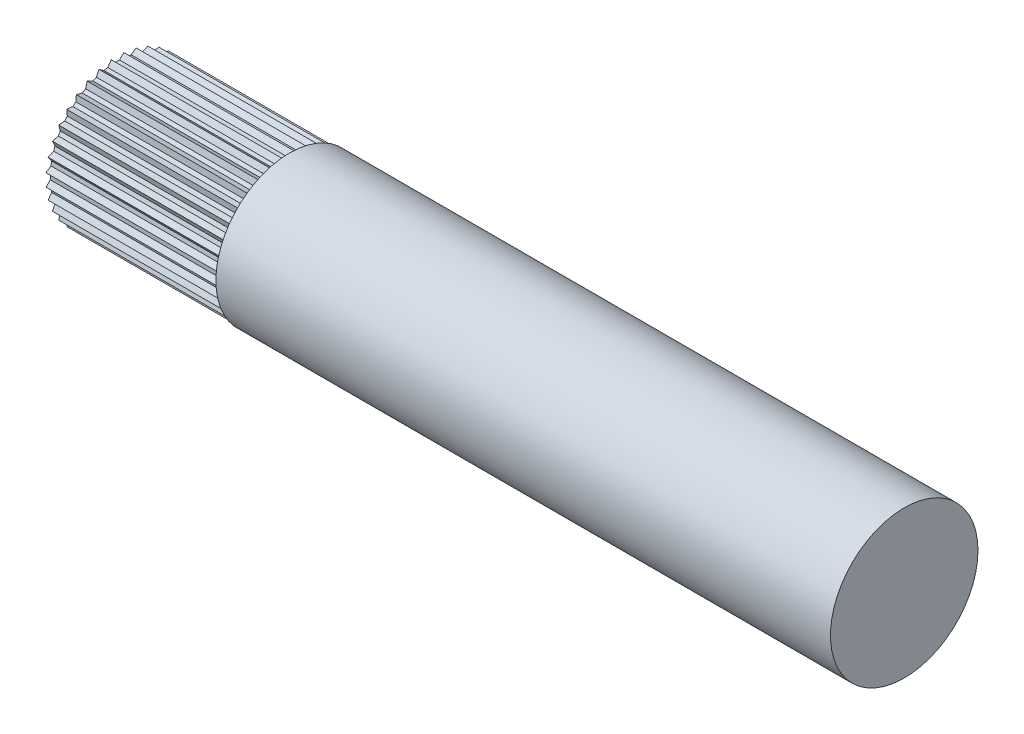
SolidWorks part; units mm, degrees
material "AISI 1020 Steel, Cold Rolled"
ref_plane "X-Y Datum" through (0, 0, 0) normal (0, 0, 1) x (1, 0, 0)
ref_plane "X-Z Datum" through (0, 0, 0) normal (0, 1, 0) x (1, 0, 0)
ref_plane "Y-Z Datum" through (0, 0, 0) normal (1, 0, 0) x (0, 0, -1)
sketch "Sketch1" plane through (0, 0, 0) normal (0, 1, 0) x (1, 0, 0)
  line L0 (139.925, 9.525) -> (139.925, 7.9375)
  line L1 (139.925, 7.9375) -> (19.25, 7.9375)
  line L2 (19.25, 7.9375) -> (19.25, 9.525)
  line L3 (19.25, 9.525) -> (139.925, 9.525)
  line L6 (157.324, 0) -> (-11.2643, 0) construction
  line L7 (19.25, 9.525) -> (19.25, -9.525) construction
  dimension "D1" = 1.5875
revolve "Revolve1" add sketch "Sketch1" angle 360 about L6
sketch "Sketch4" plane through (0, 0, 0) normal (1, 0, 0) x (0, 0, -1)
  line L0 (-9.2357, 0.808) -> (-8.6817, 0.254)
  line L1 (-8.6817, 0.254) -> (-8.6817, -0.254)
  line L2 (-8.6817, -0.254) -> (-9.2357, -0.808)
  line L3 (-8.6817, 0) -> (0, 0) construction
  line L4 (-8.5939, 1.2574) -> (-9.2357, 0.808)
  line L5 (-8.5057, 1.7577) -> (-8.5939, 1.2574)
  line L6 (-8.9551, 2.3995) -> (-8.5057, 1.7577)
  line L7 (-8.245, 2.7306) -> (-8.9551, 2.3995)
  line L8 (-8.0713, 3.208) -> (-8.245, 2.7306)
  line L9 (-8.4024, 3.9181) -> (-8.0713, 3.208)
  line L10 (-7.6456, 4.1209) -> (-8.4024, 3.9181)
  line L11 (-7.3916, 4.5608) -> (-7.6456, 4.1209)
  line L12 (-7.5944, 5.3176) -> (-7.3916, 4.5608)
  line L13 (-6.8138, 5.3859) -> (-7.5944, 5.3176)
  line L14 (-6.4873, 5.7751) -> (-6.8138, 5.3859)
  line L15 (-6.5556, 6.5556) -> (-6.4873, 5.7751)
  line L16 (-5.7751, 6.4873) -> (-6.5556, 6.5556)
  line L17 (-5.3859, 6.8138) -> (-5.7751, 6.4873)
  line L18 (-5.3176, 7.5944) -> (-5.3859, 6.8138)
  line L19 (-4.5608, 7.3916) -> (-5.3176, 7.5944)
  line L20 (-4.1209, 7.6456) -> (-4.5608, 7.3916)
  line L21 (-3.9181, 8.4024) -> (-4.1209, 7.6456)
  line L22 (-3.208, 8.0713) -> (-3.9181, 8.4024)
  line L23 (-2.7306, 8.245) -> (-3.208, 8.0713)
  line L24 (-2.3995, 8.9551) -> (-2.7306, 8.245)
  line L25 (-1.7577, 8.5057) -> (-2.3995, 8.9551)
  line L26 (-1.2574, 8.5939) -> (-1.7577, 8.5057)
  line L27 (-0.808, 9.2357) -> (-1.2574, 8.5939)
  line L28 (-0.254, 8.6817) -> (-0.808, 9.2357)
  line L29 (0.254, 8.6817) -> (-0.254, 8.6817)
  line L30 (0.808, 9.2357) -> (0.254, 8.6817)
  line L31 (1.2574, 8.5939) -> (0.808, 9.2357)
  line L32 (1.7577, 8.5057) -> (1.2574, 8.5939)
  line L33 (2.3995, 8.9551) -> (1.7577, 8.5057)
  line L34 (2.7306, 8.245) -> (2.3995, 8.9551)
  line L35 (3.208, 8.0713) -> (2.7306, 8.245)
  line L36 (3.9181, 8.4024) -> (3.208, 8.0713)
  line L37 (4.1209, 7.6456) -> (3.9181, 8.4024)
  line L38 (4.5608, 7.3916) -> (4.1209, 7.6456)
  line L39 (5.3176, 7.5944) -> (4.5608, 7.3916)
  line L40 (5.3859, 6.8138) -> (5.3176, 7.5944)
  line L41 (5.7751, 6.4873) -> (5.3859, 6.8138)
  line L42 (6.5556, 6.5556) -> (5.7751, 6.4873)
  line L43 (6.4873, 5.7751) -> (6.5556, 6.5556)
  line L44 (6.8138, 5.3859) -> (6.4873, 5.7751)
  line L45 (7.5944, 5.3176) -> (6.8138, 5.3859)
  line L46 (7.3916, 4.5608) -> (7.5944, 5.3176)
  line L47 (7.6456, 4.1209) -> (7.3916, 4.5608)
  line L48 (8.4024, 3.9181) -> (7.6456, 4.1209)
  line L49 (8.0713, 3.208) -> (8.4024, 3.9181)
  line L50 (8.245, 2.7306) -> (8.0713, 3.208)
  line L51 (8.9551, 2.3995) -> (8.245, 2.7306)
  line L52 (8.5057, 1.7577) -> (8.9551, 2.3995)
  line L53 (8.5939, 1.2574) -> (8.5057, 1.7577)
  line L54 (9.2357, 0.808) -> (8.5939, 1.2574)
  line L55 (8.6817, 0.254) -> (9.2357, 0.808)
  line L56 (8.6817, -0.254) -> (8.6817, 0.254)
  line L57 (9.2357, -0.808) -> (8.6817, -0.254)
  line L58 (8.5939, -1.2574) -> (9.2357, -0.808)
  line L59 (8.5057, -1.7577) -> (8.5939, -1.2574)
  line L60 (8.9551, -2.3995) -> (8.5057, -1.7577)
  line L61 (8.245, -2.7306) -> (8.9551, -2.3995)
  line L62 (8.0713, -3.208) -> (8.245, -2.7306)
  line L63 (8.4024, -3.9181) -> (8.0713, -3.208)
  line L64 (7.6456, -4.1209) -> (8.4024, -3.9181)
  line L65 (7.3916, -4.5608) -> (7.6456, -4.1209)
  line L66 (7.5944, -5.3176) -> (7.3916, -4.5608)
  line L67 (6.8138, -5.3859) -> (7.5944, -5.3176)
  line L68 (6.4873, -5.7751) -> (6.8138, -5.3859)
  line L69 (6.5556, -6.5556) -> (6.4873, -5.7751)
  line L70 (5.7751, -6.4873) -> (6.5556, -6.5556)
  line L71 (5.3859, -6.8138) -> (5.7751, -6.4873)
  line L72 (5.3176, -7.5944) -> (5.3859, -6.8138)
  line L73 (4.5608, -7.3916) -> (5.3176, -7.5944)
  line L74 (4.1209, -7.6456) -> (4.5608, -7.3916)
  line L75 (3.9181, -8.4024) -> (4.1209, -7.6456)
  line L76 (3.208, -8.0713) -> (3.9181, -8.4024)
  line L77 (2.7306, -8.245) -> (3.208, -8.0713)
  line L78 (2.3995, -8.9551) -> (2.7306, -8.245)
  line L79 (1.7577, -8.5057) -> (2.3995, -8.9551)
  line L80 (1.2574, -8.5939) -> (1.7577, -8.5057)
  line L81 (0.808, -9.2357) -> (1.2574, -8.5939)
  line L82 (0.254, -8.6817) -> (0.808, -9.2357)
  line L83 (-0.254, -8.6817) -> (0.254, -8.6817)
  line L84 (-0.808, -9.2357) -> (-0.254, -8.6817)
  line L85 (-1.2574, -8.5939) -> (-0.808, -9.2357)
  line L86 (-1.7577, -8.5057) -> (-1.2574, -8.5939)
  line L87 (-2.3995, -8.9551) -> (-1.7577, -8.5057)
  line L88 (-2.7306, -8.245) -> (-2.3995, -8.9551)
  line L89 (-3.208, -8.0713) -> (-2.7306, -8.245)
  line L90 (-3.9181, -8.4024) -> (-3.208, -8.0713)
  line L91 (-4.1209, -7.6456) -> (-3.9181, -8.4024)
  line L92 (-4.5608, -7.3916) -> (-4.1209, -7.6456)
  line L93 (-5.3176, -7.5944) -> (-4.5608, -7.3916)
  line L94 (-5.3859, -6.8138) -> (-5.3176, -7.5944)
  line L95 (-5.7751, -6.4873) -> (-5.3859, -6.8138)
  line L96 (-6.5556, -6.5556) -> (-5.7751, -6.4873)
  line L97 (-6.4873, -5.7751) -> (-6.5556, -6.5556)
  line L98 (-6.8138, -5.3859) -> (-6.4873, -5.7751)
  line L99 (-7.5944, -5.3176) -> (-6.8138, -5.3859)
  line L100 (-7.3916, -4.5608) -> (-7.5944, -5.3176)
  line L101 (-7.6456, -4.1209) -> (-7.3916, -4.5608)
  line L102 (-8.4024, -3.9181) -> (-7.6456, -4.1209)
  line L103 (-8.0713, -3.208) -> (-8.4024, -3.9181)
  line L104 (-8.245, -2.7306) -> (-8.0713, -3.208)
  line L105 (-8.9551, -2.3995) -> (-8.245, -2.7306)
  line L106 (-8.5057, -1.7577) -> (-8.9551, -2.3995)
  line L107 (-8.5939, -1.2574) -> (-8.5057, -1.7577)
  line L108 (-9.2357, -0.808) -> (-8.5939, -1.2574)
  circle A0 centre (0, 0) radius 8.6854 construction
  circle A1 centre (0, 0) radius 9.271 construction
  circle A2 centre (0, 0) radius 12.7
  point P155 (0, 0)
  dimension "D1" = 18.542
  dimension "D2" = 0.508
  dimension "D3" = 17.3708
  dimension "D6" = 25.4
  dimension "D4" = 135
  dimension "D5" = 1.616
  dimension "D7" = 36
extrude "Cut-Extrude2" cut sketch "Sketch4" along normal blind 22.225 from surface at 19.25 starting at face at (19.25, 0, -7.9375)
sketch "Sketch6" plane through (19.25, 0, 0) normal (-1, 0, 0) x (0, 0, 1)
  circle A0 centre (0, 0) radius 7.9375
  dimension "D1" = 15.875
extrude "Boss-Extrude1" add sketch "Sketch6" against normal blind 101.6
sketch "Sketch7" plane through (120.85, 0, 0) normal (1, 0, 0) x (0, 0, -1)
  circle A0 centre (0, 0) radius 23.308
extrude "Cut-Extrude3" cut sketch "Sketch7" along normal up to surface (19.075 mm away) up to face at (139.925, 0, -9.525)
